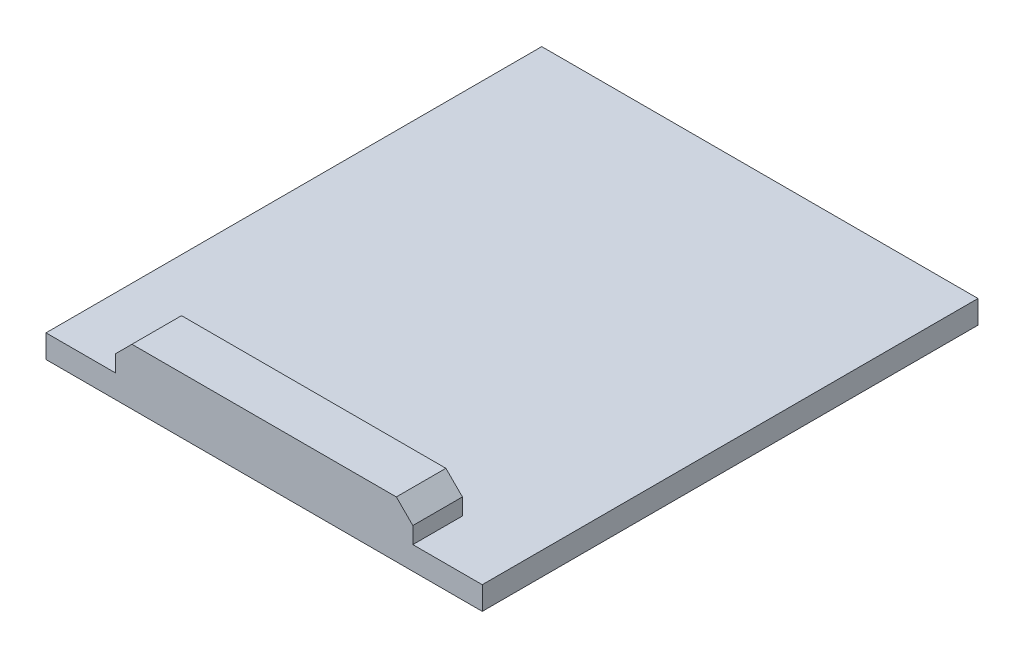
SolidWorks part; units mm, degrees
material "1023 Carbon Steel Sheet (SS)"
ref_plane "Alzado" through (0, 0, 0) normal (0, 0, 1) x (1, 0, 0)
ref_plane "Planta" through (0, 0, 0) normal (0, 1, 0) x (1, 0, 0)
ref_plane "Vista lateral" through (0, 0, 0) normal (1, 0, 0) x (0, 0, -1)
sketch "Sketch1" plane through (0, 0, 0) normal (0, 0, 1) x (1, 0, 0)
  line L0 (0, 0) -> (26.4, 0)
  line L1 (26.4, 0) -> (26.4, 1.4)
  line L2 (26.4, 1.4) -> (0, 1.4)
  line L3 (0, 1.4) -> (0, 0)
  dimension "D1" = 26.4
  dimension "D2" = 1.4
extrude "Boss-Extrude1" add sketch "Sketch1" along normal blind 30
sketch "Sketch2" plane through (0, 0, 30) normal (0, 0, 1) x (1, 0, 0)
  line L0 (4.2, 1.4) -> (4.2, 2.4)
  line L1 (26.4, 1.4) -> (0, 1.4) construction
  line L2 (4.2, 2.4) -> (5.2, 3.4)
  line L3 (5.2, 3.4) -> (21.2, 3.4)
  line L4 (21.2, 3.4) -> (22.2, 2.4)
  line L5 (22.2, 2.4) -> (22.2, 1.4)
  line L6 (22.2, 1.4) -> (4.2, 1.4)
  line L7 (4.2, 2.4) -> (22.2, 2.4) construction
  line L8 (0, 0) -> (26.4, 0) construction
  point P10 (13.2, 0)
  point P11 (13.2, 3.4)
  dimension "D1" = 18
  dimension "D2" = 1
  dimension "D3" = 1
  dimension "D4" = 45
  dimension "D5" = 45
  dimension "D6" = 2
extrude "Boss-Extrude2" add sketch "Sketch2" against normal blind 3
